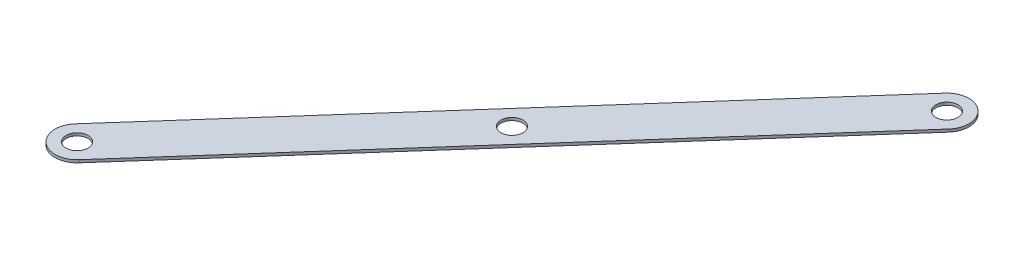
SolidWorks part; units mm, degrees
ref_plane "Front" through (0, 0, 0) normal (0, 0, 1) x (1, 0, 0)
ref_plane "Top" through (0, 0, 0) normal (0, 1, 0) x (1, 0, 0)
ref_plane "Right" through (0, 0, 0) normal (1, 0, 0) x (0, 0, -1)
sketch "Sketch1" plane through (0, 0, 0) normal (0, 1, 0) x (1, 0, 0)
  line L0 (0, 0) -> (235.6337, 266.3234) construction
  line L1 (-9.5115, 8.4155) -> (226.1221, 274.7388)
  line L2 (9.5115, -8.4155) -> (245.1452, 257.9079)
  arc A0 (-9.5115, 8.4155) -> (9.5115, -8.4155) centre (0, 0) ccw
  arc A1 (245.1452, 257.9079) -> (226.1221, 274.7388) centre (235.6337, 266.3234) ccw
  circle A2 centre (117.8168, 133.1617) radius 6.35
  circle A3 centre (235.6337, 266.3234) radius 6.35
  circle A4 centre (0, 0) radius 6.35
  point P3 (117.8168, 133.1617)
  dimension "D3" = 12.7
  dimension "D4" = 12.7
  dimension "D5" = 12.7
  dimension "D1" = 355.6
  dimension "D2" = 25.4
extrude "Boss-Extrude1" add sketch "Sketch1" along normal blind 1.5875
